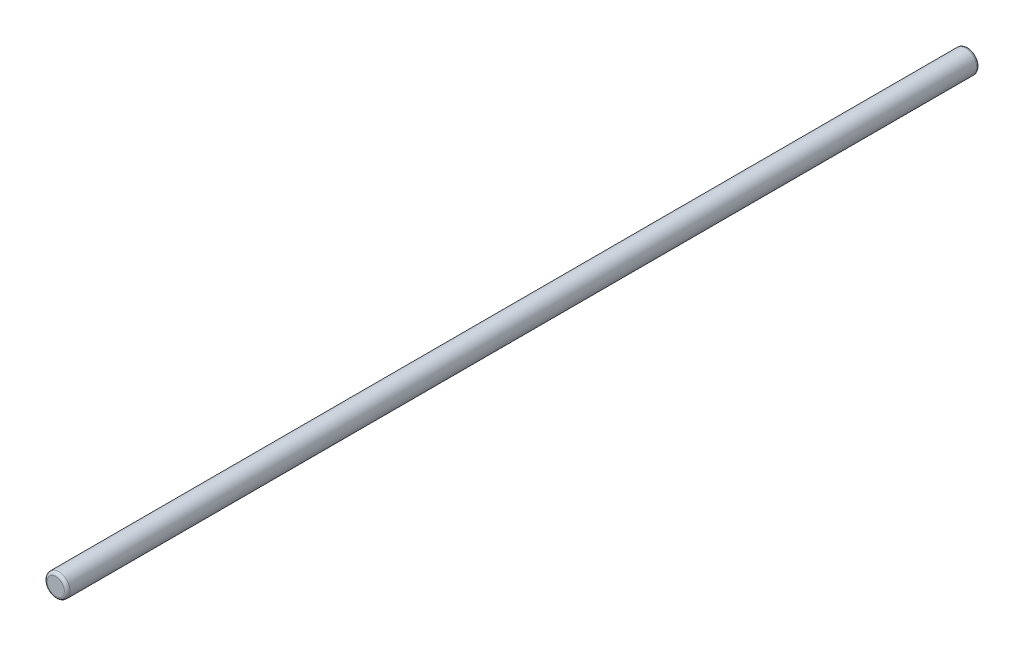
SolidWorks part; units mm, degrees
ref_plane "Front Plane" through (0, 0, 0) normal (0, 0, 1) x (1, 0, 0)
ref_plane "Top Plane" through (0, 0, 0) normal (0, 1, 0) x (1, 0, 0)
ref_plane "Right Plane" through (0, 0, 0) normal (1, 0, 0) x (0, 0, -1)
sketch "Sketch1" plane through (0, 0, 0) normal (0, 0, 1) x (1, 0, 0)
  circle A0 centre (0, 0) radius 4
extrude "Extrude2" add sketch "Sketch1" along normal blind 318.625
cosmetic thread "Cosmetic Thread2" parameters "D2"=7
fillet "Fillet2" radius 1 1 edges at (4, 0, 0)
fillet "Fillet3" radius 1 1 edges at (4, 0, 318.625)
